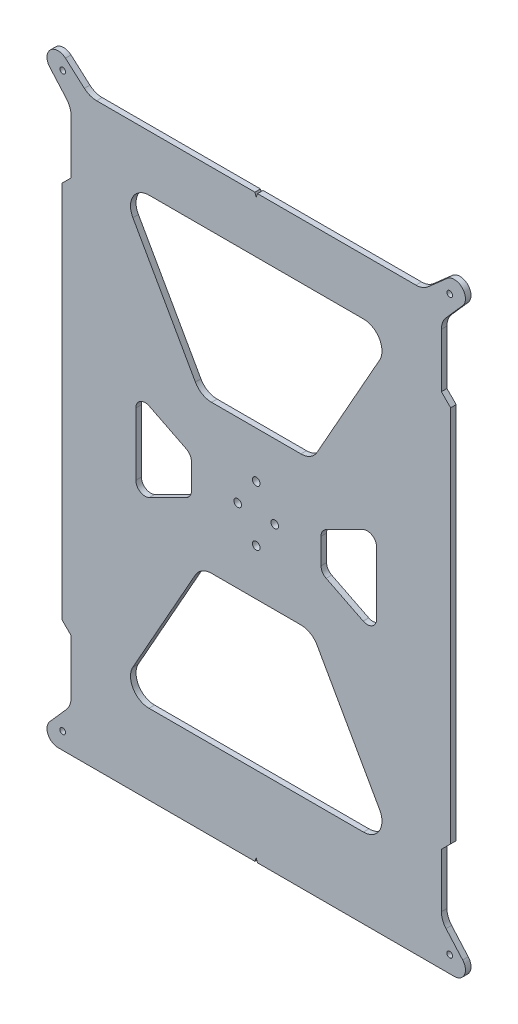
SolidWorks part; units mm, degrees
material "Aleación 1060"
ref_plane "Front Plane" through (0, 0, 0) normal (0, 0, 1) x (1, 0, 0)
ref_plane "Top Plane" through (0, 0, 0) normal (0, 1, 0) x (1, 0, 0)
ref_plane "Right Plane" through (0, 0, 0) normal (1, 0, 0) x (0, 0, -1)
sketch "Model" plane through (0, 0, 0) normal (0, 0, 1) x (1, 0, 0)
  line L21 (24.1515, -40) -> (-24.1515, -40)
  line L22 (-32.8673, -45.0974) -> (-66.6173, -105.0974)
  line L23 (-57.9015, -120) -> (57.9015, -120)
  line L24 (66.6173, -105.0974) -> (32.8673, -45.0974)
  line L25 (32.8673, 45.0974) -> (66.6173, 105.0974)
  line L26 (57.9015, 120) -> (-57.9015, 120)
  line L27 (-66.6173, 105.0974) -> (-32.8673, 45.0974)
  line L28 (-24.1515, 40) -> (24.1515, 40)
  line L29 (-37.7639, 11.382) -> (-57.7639, 21.382)
  line L30 (-65, 16.9098) -> (-65, -16.9098)
  line L31 (-57.7639, -21.382) -> (-37.7639, -11.382)
  line L32 (-35, -6.9098) -> (-35, 6.9098)
  line L33 (37.7639, -11.382) -> (57.7639, -21.382)
  line L34 (65, -16.9098) -> (65, 16.9098)
  line L35 (57.7639, 21.382) -> (37.7639, 11.382)
  line L36 (35, 6.9098) -> (35, -6.9098)
  line L37 (-102.5021, -142.8353) -> (-111.4987, -153.0299)
  line L38 (-100, -136.2185) -> (-100, -107)
  line L39 (-105, -102) -> (-100, -107)
  line L40 (-105, 102) -> (-105, -102)
  line L41 (-100, 107) -> (-105, 102)
  line L42 (-100, 107) -> (-100, 136.2185)
  line L43 (-102.5021, 142.8353) -> (-111.4987, 153.0299)
  line L44 (-92.8353, 152.5021) -> (-103.0299, 161.4987)
  line L45 (-86.2185, 150) -> (-0.6974, 150)
  line L46 (-0.6974, 150) -> (0, 148)
  line L47 (0, 148) -> (0.7013, 150)
  line L48 (0.7013, 150) -> (86.2185, 150)
  line L49 (92.8353, 152.5021) -> (103.0299, 161.4987)
  line L50 (102.5021, 142.8353) -> (111.4987, 153.0299)
  line L51 (100, 107) -> (100, 136.2185)
  line L52 (105, 102) -> (100, 107)
  line L53 (105, -102) -> (105, 102)
  line L54 (100, -107) -> (105, -102)
  line L55 (100, -136.2185) -> (100, -107)
  line L56 (102.5021, -142.8353) -> (111.4987, -153.0299)
  line L57 (0.6995, -163) -> (107, -163)
  line L58 (0, -160.9967) -> (0.6995, -163)
  line L59 (-0.7007, -163) -> (0, -160.9967)
  line L60 (-107, -163) -> (-0.7007, -163)
  circle A0 centre (-104.5, -154) radius 1.55 construction
  circle A1 centre (-104.5, -154) radius 1.55
  circle A2 centre (104.5, -154) radius 1.55 construction
  circle A3 centre (104.5, -154) radius 1.55
  arc A4 (-57.9015, 120) -> (-66.6173, 105.0974) centre (-57.9015, 110) ccw
  arc A5 (66.6173, 105.0974) -> (57.9015, 120) centre (57.9015, 110) ccw
  arc A6 (-32.8673, 45.0974) -> (-24.1515, 40) centre (-24.1515, 50) ccw
  arc A7 (32.8673, 45.0974) -> (24.1515, 40) centre (24.1515, 50) cw
  arc A8 (57.7639, -21.382) -> (65, -16.9098) centre (60, -16.9098) ccw
  arc A9 (65, 16.9098) -> (57.7639, 21.382) centre (60, 16.9098) ccw
  arc A10 (37.7639, -11.382) -> (35, -6.9098) centre (40, -6.9098) cw
  arc A11 (37.7639, 11.382) -> (35, 6.9098) centre (40, 6.9098) ccw
  arc A12 (-37.7639, -11.382) -> (-35, -6.9098) centre (-40, -6.9098) ccw
  arc A13 (-37.7639, 11.382) -> (-35, 6.9098) centre (-40, 6.9098) cw
  arc A14 (-65, -16.9098) -> (-57.7639, -21.382) centre (-60, -16.9098) ccw
  arc A15 (-57.7639, 21.382) -> (-65, 16.9098) centre (-60, 16.9098) ccw
  circle A16 centre (-10, 0) radius 2.05
  circle A17 centre (0, -15) radius 2.05
  circle A18 centre (10, 0) radius 2.05
  circle A19 centre (0, 15) radius 2.05
  circle A20 centre (104.5, 155) radius 1.55 construction
  circle A21 centre (104.5, 155) radius 1.55
  arc A22 (-66.6173, -105.0974) -> (-57.9015, -120) centre (-57.9015, -110) ccw
  arc A23 (57.9015, -120) -> (66.6173, -105.0974) centre (57.9015, -110) ccw
  arc A24 (-102.5021, -142.8353) -> (-100, -136.2185) centre (-110, -136.2185) ccw
  arc A25 (-100, 136.2185) -> (-102.5021, 142.8353) centre (-110, 136.2185) ccw
  arc A26 (-103.0299, 161.4987) -> (-111.4987, 153.0299) centre (-107, 157) ccw
  arc A27 (-92.8353, 152.5021) -> (-86.2185, 150) centre (-86.2185, 160) ccw
  arc A28 (86.2185, 150) -> (92.8353, 152.5021) centre (86.2185, 160) ccw
  arc A29 (111.4987, 153.0299) -> (103.0299, 161.4987) centre (107, 157) ccw
  arc A30 (102.5021, 142.8353) -> (100, 136.2185) centre (110, 136.2185) ccw
  arc A31 (100, -136.2185) -> (102.5021, -142.8353) centre (110, -136.2185) ccw
  arc A32 (107, -163) -> (111.4987, -153.0299) centre (107, -157) ccw
  arc A33 (-111.4987, -153.0299) -> (-107, -163) centre (-107, -157) ccw
  circle A35 centre (-104.5, 155) radius 1.55 construction
  circle A36 centre (-104.5, 155) radius 1.55
  arc A37 (24.1515, -40) -> (32.8673, -45.0974) centre (24.1515, -50) cw
  arc A38 (-24.1515, -40) -> (-32.8673, -45.0974) centre (-24.1515, -50) ccw
  point P12 (0, 0)
  dimension "D1" = 10
  dimension "D2" = 10
  dimension "D3" = 10
  dimension "D4" = 5
  dimension "D5" = 10
extrude "Saliente-Extruir1" add sketch "Model" along normal blind 3
